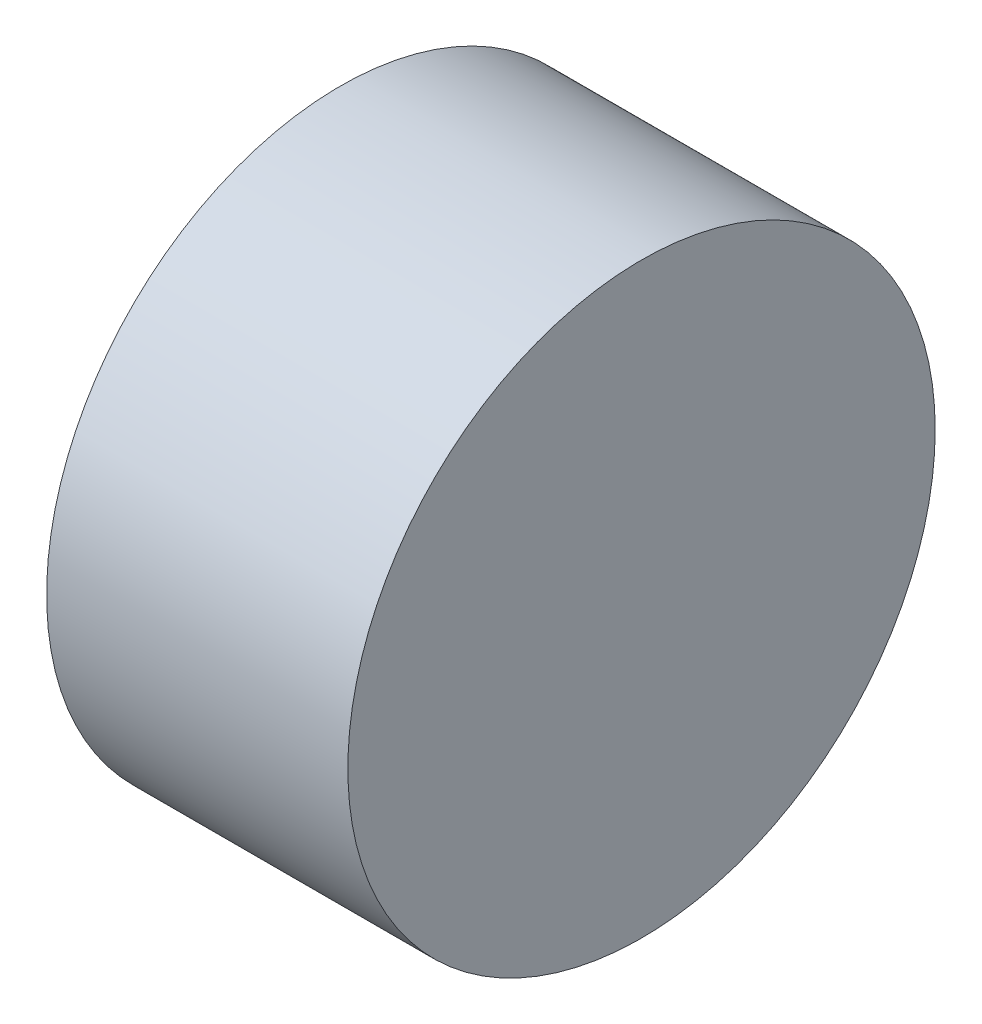
SolidWorks part; units mm, degrees
material "ПК/АБС"
ref_plane "Спереди" through (0, 0, 0) normal (0, 0, 1) x (1, 0, 0)
ref_plane "Сверху" through (0, 0, 0) normal (0, 1, 0) x (1, 0, 0)
ref_plane "Справа" through (0, 0, 0) normal (1, 0, 0) x (0, 0, -1)
sketch "Эскиз1" plane through (0, 0, 0) normal (1, 0, 0) x (0, 0, -1)
  circle A0 centre (0, 0) radius 7.8
extrude "Бобышка-Вытянуть1" add sketch "Эскиз1" along normal blind 8
sketch "Эскиз2" plane through (0, 0, 0) normal (-1, 0, 0) x (0, 0, 1)
  circle A0 centre (0, 0) radius 1.5
extrude "Вырез-Вытянуть1" cut sketch "Эскиз2" against normal blind 1
